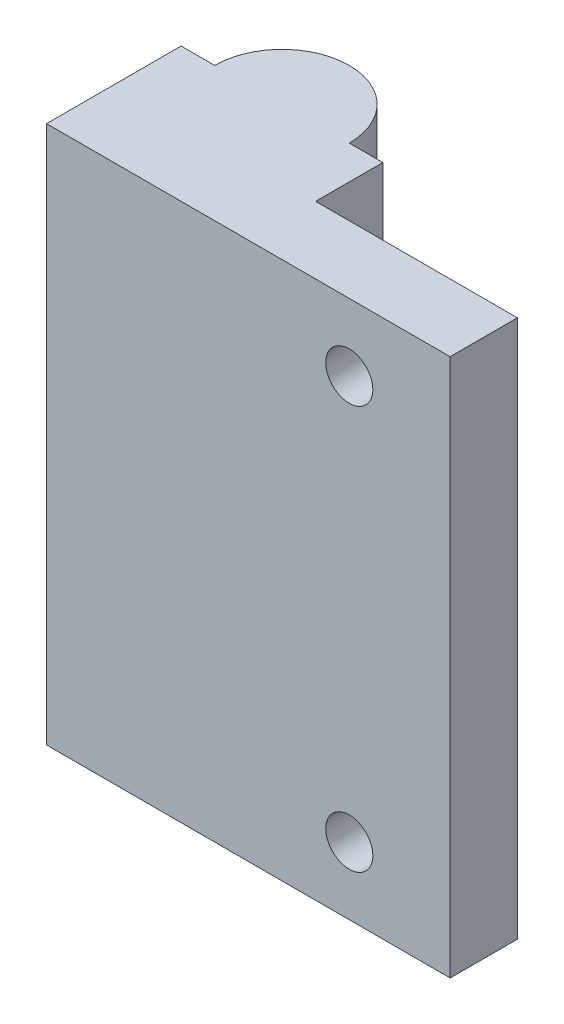
SolidWorks part; units mm, degrees
ref_plane "Front Plane" through (0, 0, 0) normal (0, 0, 1) x (1, 0, 0)
ref_plane "Top Plane" through (0, 0, 0) normal (0, 1, 0) x (1, 0, 0)
ref_plane "Right Plane" through (0, 0, 0) normal (1, 0, 0) x (0, 0, -1)
sketch "Sketch1" plane through (0, 0, 0) normal (0, 0, 1) x (1, 0, 0)
  line L1 (0, 0) -> (30, 0)
  line L2 (0, 0) -> (0, 40)
  line L3 (0, 40) -> (30, 40)
  line L4 (30, 0) -> (30, 40)
  dimension "D1" = 30
  dimension "D2" = 40
extrude "Boss-Extrude1" add sketch "Sketch1" along normal blind 10
sketch "Sketch2" plane through (0, 0, 0) normal (0, 0, -1) x (-1, 0, 0)
  line L0 (-30, 40) -> (0, 40) construction
  line L1 (-30, 0) -> (-15, 0)
  line L2 (-30, 0) -> (-30, 40)
  line L3 (-30, 40) -> (-15, 40)
  line L4 (-15, 0) -> (-15, 40)
  line L5 (0, 0) -> (-30, 0) construction
  dimension "D1" = 15
extrude "Cut-Extrude1" cut sketch "Sketch2" against normal blind 5
sketch "Sketch4" plane through (0, 0, 5) normal (0, 0, -1) x (-1, 0, 0)
  line L0 (-30, 20) -> (-21.2468, 20) construction
  line L1 (-30, 40) -> (-30, 0) construction
  line L2 (-30, 0) -> (-15, 0) construction
  circle A0 centre (-22.5, 5) radius 1.75
  circle A1 centre (-22.5, 35) radius 1.75
  point P10 (-22.5, 0)
  dimension "D2" = 3.5
  dimension "D1" = 30
extrude "Cut-Extrude3" cut sketch "Sketch4" against normal blind 30
sketch "Sketch7" plane through (0, 0, 0) normal (0, -1, 0) x (1, 0, 0)
  line L0 (0, 0) -> (15, 0) construction
  circle A0 centre (7.5, 0) radius 5
  dimension "D1" = 10
extrude "Boss-Extrude2" add sketch "Sketch7" against normal blind 40
sketch "Sketch8" plane through (0, 0, 0) normal (0, -1, 0) x (1, 0, 0)
  circle A0 centre (7.5, 0) radius 3.5
  dimension "D1" = 7
extrude "Cut-Extrude4" cut sketch "Sketch8" against normal blind 30
